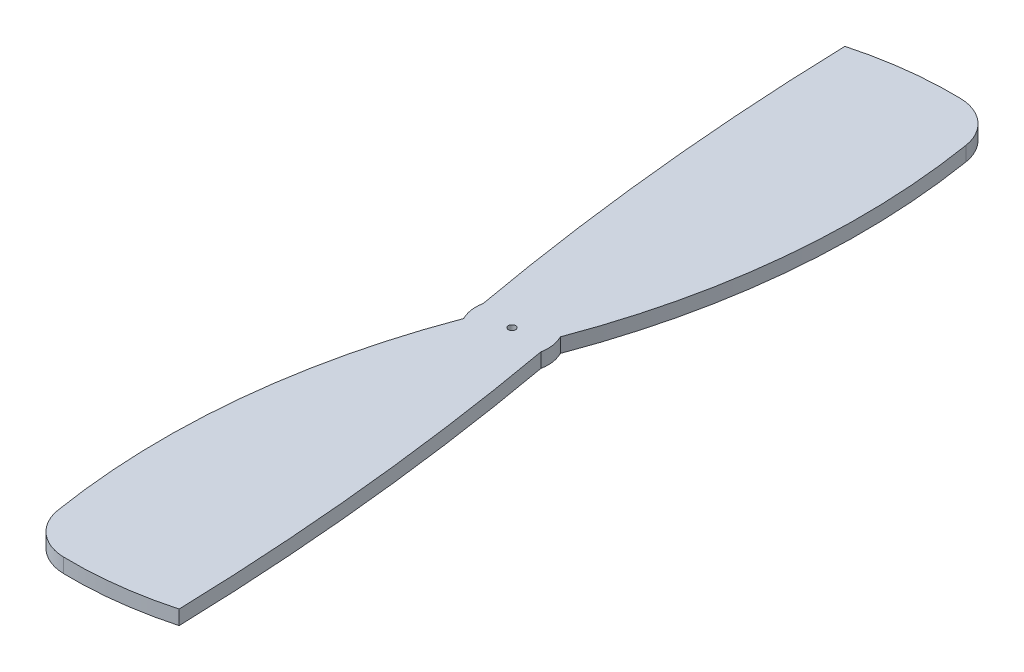
SolidWorks part; units mm, degrees
ref_plane "Front Plane" through (0, 0, 0) normal (0, 0, 1) x (1, 0, 0)
ref_plane "Top Plane" through (0, 0, 0) normal (0, 1, 0) x (1, 0, 0)
ref_plane "Right Plane" through (0, 0, 0) normal (1, 0, 0) x (0, 0, -1)
sketch "Sketch1" plane through (0, 0, 0) normal (0, 1, 0) x (1, 0, 0)
  line L3 (-4.35, 0) -> (-4.35, 47) construction
  line L4 (-4.35, 23.5) -> (-9.7634, 23.5) construction
  arc A0 (-2.3836, 23.1347) -> (-2.566, 24.4041) centre (-4.35, 23.5) ccw
  circle A1 centre (-4.35, 23.5) radius 0.2
  arc A2 (-6.3164, 23.8653) -> (-6.134, 22.5959) centre (-4.35, 23.5) ccw
  arc A3 (-5.77, 0.0044) -> (-0.0592, 0.7125) centre (-5.35, 20) ccw
  arc A4 (-6.134, 22.5959) -> (-8.1853, 2.1041) centre (31.3, 8.5) ccw
  arc A6 (-8.1853, 2.1041) -> (-5.77, 0.0044) centre (-5.7175, 2.5039) ccw
  arc A8 (-0.0592, 0.7125) -> (-2.3836, 23.1347) centre (-150, -3.5) ccw
  arc A11 (-2.566, 24.4041) -> (-0.5147, 44.8959) centre (-40, 38.5) ccw
  arc A12 (-0.5147, 44.8959) -> (-2.93, 46.9956) centre (-2.9825, 44.4961) ccw
  arc A13 (-2.93, 46.9956) -> (-8.6408, 46.2875) centre (-3.35, 27) ccw
  arc A14 (-8.6408, 46.2875) -> (-6.3164, 23.8653) centre (141.3, 50.5) ccw
  dimension "D4" = 0.4
  dimension "D5" = 4
extrude "Boss-Extrude1" add sketch "Sketch1" along normal blind 0.8
